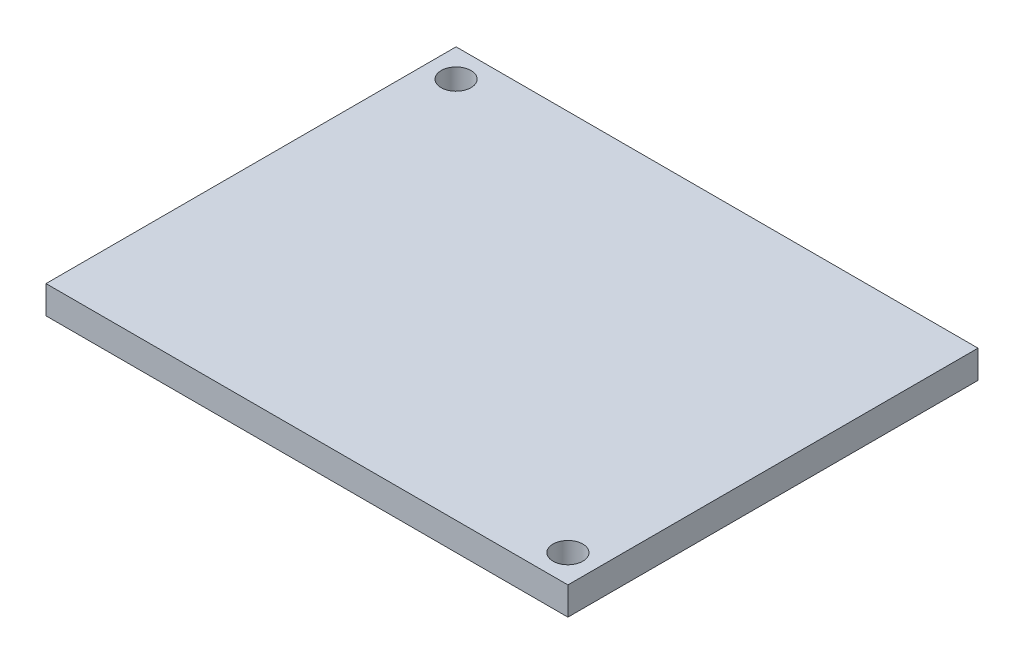
SolidWorks part; units mm, degrees
ref_plane "Front Plane" through (0, 0, 0) normal (0, 0, 1) x (1, 0, 0)
ref_plane "Top Plane" through (0, 0, 0) normal (0, 1, 0) x (1, 0, 0)
ref_plane "Right Plane" through (0, 0, 0) normal (1, 0, 0) x (0, 0, -1)
sketch "Sketch1" plane through (0, 0, 0) normal (0, 1, 0) x (1, 0, 0)
  line L1 (-535.4496, 356.2954) -> (-479.4496, 356.2954)
  line L2 (-535.4496, 356.2954) -> (-535.4496, 312.2954)
  line L3 (-535.4496, 312.2954) -> (-479.4496, 312.2954)
  line L4 (-479.4496, 356.2954) -> (-479.4496, 312.2954)
  dimension "D1" = 56
  dimension "D2" = 44
extrude "Boss-Extrude1" add sketch "Sketch1" along normal blind 3
sketch "Sketch2" plane through (0, 3, 0) normal (0, 1, 0) x (1, 0, 0)
  line L0 (-479.4496, 356.2954) -> (-535.4496, 356.2954) construction
  line L2 (-535.4496, 356.2954) -> (-535.4496, 312.2954) construction
  circle A0 centre (-532.4496, 353.2954) radius 1.6
  dimension "D1" = 3
  dimension "D2" = 3
extrude "Cut-Extrude1" cut sketch "Sketch2" against normal blind 3
sketch "Sketch4" plane through (0, 3, 0) normal (0, 1, 0) x (1, 0, 0)
  line L0 (-479.4496, 312.2954) -> (-479.4496, 356.2954) construction
  line L1 (-535.4496, 312.2954) -> (-479.4496, 312.2954) construction
  circle A0 centre (-482.4496, 315.2954) radius 1.6
  dimension "D1" = 3
  dimension "D2" = 3
extrude "Cut-Extrude2" cut sketch "Sketch4" against normal blind 3
